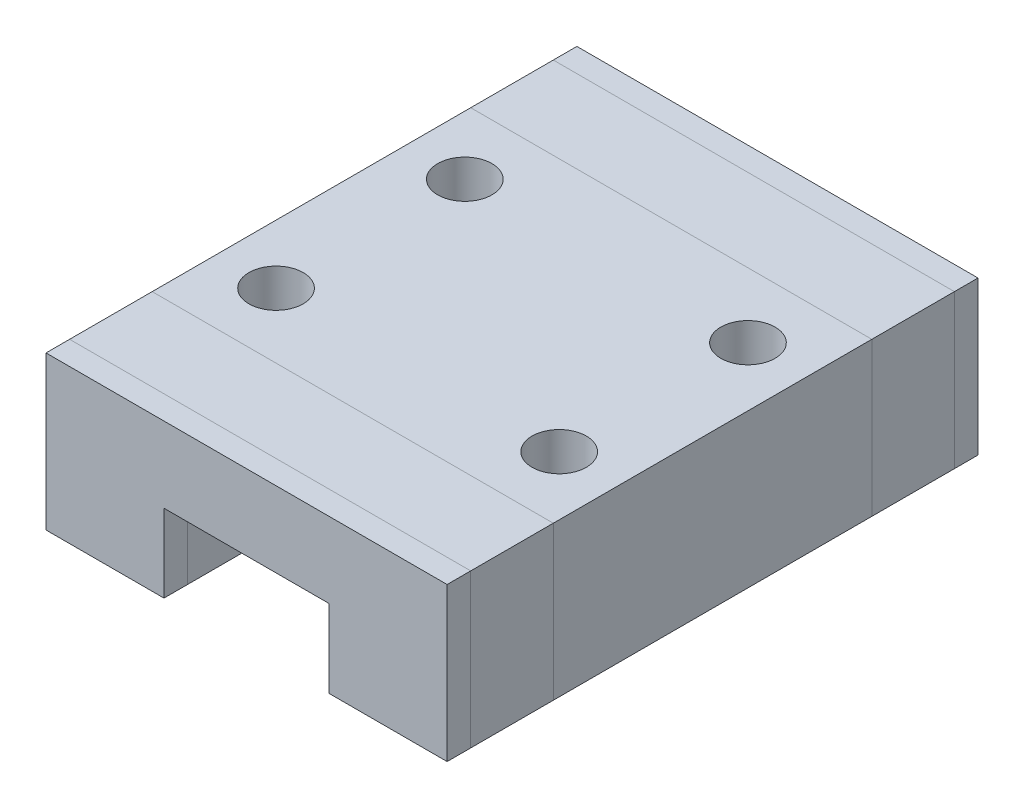
SolidWorks part; units mm, degrees
ref_plane "前视基准面" through (0, 0, 0) normal (0, 0, 1) x (1, 0, 0)
ref_plane "上视基准面" through (0, 0, 0) normal (0, 1, 0) x (1, 0, 0)
ref_plane "右视基准面" through (0, 0, 0) normal (1, 0, 0) x (0, 0, -1)
sketch "草图1" plane through (0, 0, 0) normal (0, 0, 1) x (1, 0, 0)
  line L1 (-8.5, -3.25) -> (8.5, -3.25)
  line L2 (-8.5, -3.25) -> (-8.5, 3.25)
  line L3 (-8.5, 3.25) -> (8.5, 3.25)
  line L4 (8.5, -3.25) -> (8.5, 3.25)
  line L5 (-8.5, -3.25) -> (8.5, 3.25) construction
  line L6 (-8.5, 3.25) -> (8.5, -3.25) construction
  point P0 (0, 0)
  dimension "D1" = 6.5
  dimension "D2" = 17
extrude "凸台-拉伸1" add sketch "草图1" along normal blind 22.5
sketch "草图2" plane through (0, 0, 22.5) normal (0, 0, 1) x (1, 0, 0)
  line L0 (-3.5, -3.25) -> (-3.5, 0.05)
  line L1 (-8.5, -3.25) -> (8.5, -3.25) construction
  line L2 (-3.5, 0.05) -> (3.5, 0.05)
  line L3 (3.5, 0.05) -> (3.5, -3.25)
  line L4 (3.5, -3.25) -> (-3.5, -3.25)
  line L5 (0, 15.2831) -> (0, -7.6728) construction
  line L6 (8.5, 3.25) -> (-8.5, 3.25) construction
  dimension "D1" = 7
  dimension "D2" = 3.2
extrude "切除-拉伸1" cut sketch "草图2" against normal through all
sketch "草图3" plane through (0, 3.25, 0) normal (0, 1, 0) x (1, 0, 0)
  line L0 (0, 9.5189) -> (0, -29.7226) construction
  line L1 (-15.309, -11.25) -> (23.995, -11.25) construction
  line L2 (8.5, -22.5) -> (-8.5, -22.5) construction
  line L3 (8.5, 0) -> (-8.5, 0) construction
  circle A0 centre (-6, -7.25) radius 1.15
  circle A3 centre (-6, -15.25) radius 1.15
  circle A4 centre (6, -15.25) radius 1.15
  circle A5 centre (6, -7.25) radius 1.15
  dimension "D1" = 8
  dimension "D2" = 12
  dimension "D3" = 2.3
extrude "切除-拉伸2" cut sketch "草图3" against normal blind 4
sketch "草图4" plane through (0, 3.25, 0) normal (0, 1, 0) x (1, 0, 0)
  line L0 (-8.5, -11.25) -> (15.1018, -11.25) construction
  line L1 (-8.5, -22.5) -> (-8.5, 0) construction
  line L2 (-8.5, -18) -> (8.5, -18)
  line L3 (8.5, -22.5) -> (8.5, 0) construction
  line L4 (-8.5, -21.5) -> (8.5, -21.5)
  line L5 (-8.5, -1) -> (8.5, -1)
  line L6 (-8.5, -4.5) -> (8.5, -4.5)
  line L7 (8.5, -22.5) -> (-8.5, -22.5) construction
  dimension "D1" = 13.5
  dimension "D2" = 1
split line "分割线1"
